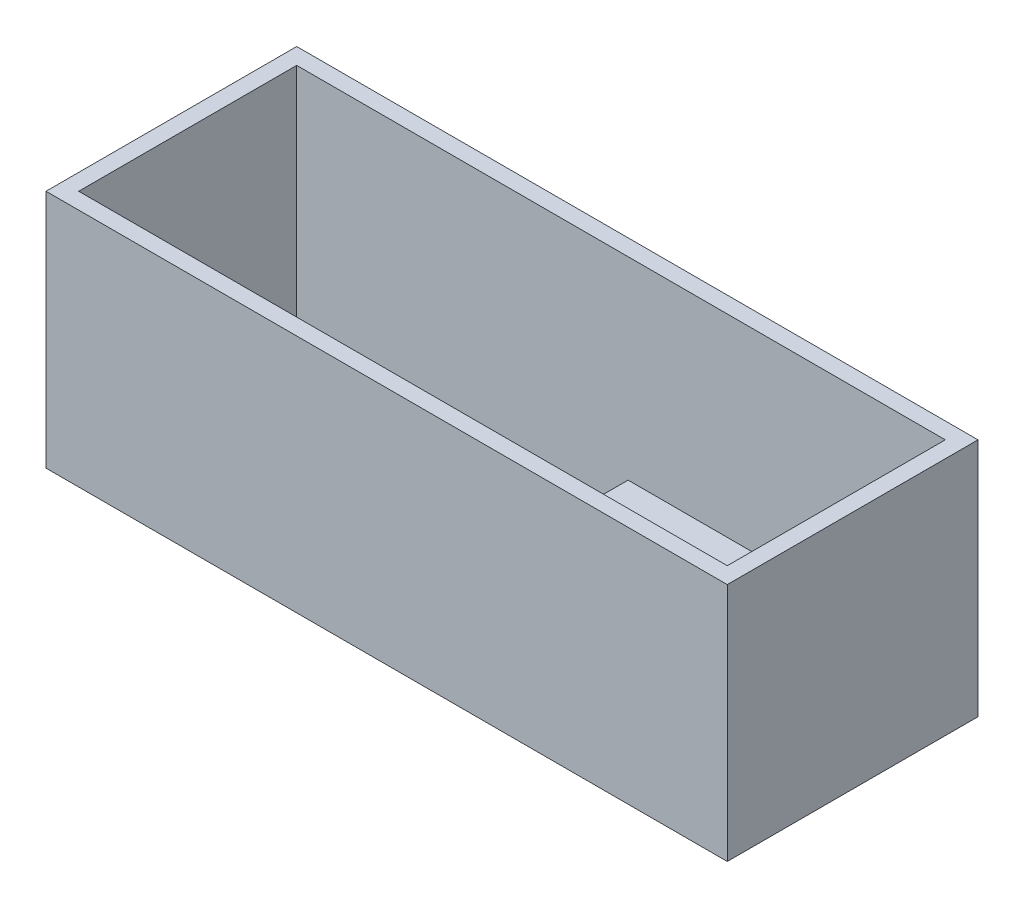
SolidWorks part; units mm, degrees
ref_plane "Front Plane" through (0, 0, 0) normal (0, 0, 1) x (1, 0, 0)
ref_plane "Top Plane" through (0, 0, 0) normal (0, 1, 0) x (1, 0, 0)
ref_plane "Right Plane" through (0, 0, 0) normal (1, 0, 0) x (0, 0, -1)
sketch "Sketch1" plane through (0, 0, 0) normal (0, 1, 0) x (1, 0, 0)
  line L1 (-59.5, -20) -> (59.5, -20)
  line L2 (-59.5, -20) -> (-59.5, 20)
  line L3 (-59.5, 20) -> (59.5, 20)
  line L4 (59.5, -20) -> (59.5, 20)
  line L5 (-59.5, -20) -> (59.5, 20) construction
  line L6 (-59.5, 20) -> (59.5, -20) construction
  point P0 (0, 0)
  dimension "D1" = 119
  dimension "D2" = 40
extrude "Boss-Extrude1" add sketch "Sketch1" along normal blind 4
sketch "Sketch2" plane through (0, 0, 0) normal (0, 1, 0) x (1, 0, 0)
  line L1 (59.5, -20) -> (-59.5, -20)
  line L2 (59.5, -20) -> (59.5, 20)
  line L3 (59.5, 20) -> (-59.5, 20)
  line L4 (-59.5, -20) -> (-59.5, 20)
  line L5 (59.5, -20) -> (-59.5, 20) construction
  line L6 (59.5, 20) -> (-59.5, -20) construction
  line L7 (-62.5, -23) -> (62.5, -23)
  line L8 (-62.5, -23) -> (-62.5, 23)
  line L9 (-62.5, 23) -> (62.5, 23)
  line L10 (62.5, -23) -> (62.5, 23)
  line L11 (-62.5, -23) -> (62.5, 23) construction
  line L12 (-62.5, 23) -> (62.5, -23) construction
  point P0 (0, 0)
  point P7 (0, 0)
  dimension "D1" = 3
  dimension "D2" = 3
extrude "Boss-Extrude2" add sketch "Sketch2" along normal blind 44
sketch "Sketch3" plane through (0, 4, 0) normal (0, 1, 0) x (1, 0, 0)
  line L0 (-59.5, -20) -> (59.5, -20) construction
  line L1 (1.3, -20) -> (59.5, -20)
  line L2 (1.3, -20) -> (1.3, 20)
  line L3 (1.3, 20) -> (59.5, 20)
  line L4 (59.5, -20) -> (59.5, 20)
  dimension "D1" = 58.2
extrude "Boss-Extrude3" add sketch "Sketch3" along normal blind 3
sketch "Sketch4" plane through (0, 7, 0) normal (0, 1, 0) x (1, 0, 0)
  line L0 (1.3, -20) -> (59.5, -20) construction
  line L1 (1.3, 20) -> (29.3, 20)
  line L2 (1.3, 20) -> (1.3, -20)
  line L3 (1.3, -20) -> (29.3, -20)
  line L4 (29.3, 20) -> (29.3, -20)
  dimension "D1" = 28
extrude "Boss-Extrude4" add sketch "Sketch4" along normal blind 1.5
sketch "Sketch5" plane through (0, 0, 0) normal (0, -1, 0) x (1, 0, 0)
  line L0 (62.5, -23) -> (-62.5, -23) construction
  line L1 (62.5, 23) -> (62.5, -23) construction
  circle A0 centre (39.5, 0) radius 4
  dimension "D1" = 8
  dimension "D2" = 23
  dimension "D3" = 23
extrude "Boss-Extrude5" add sketch "Sketch5" along normal blind 12
sketch "Sketch6" plane through (0, 0, 0) normal (0, -1, 0) x (1, 0, 0)
  circle A0 centre (39.5, 0) radius 11.5
  circle A1 centre (39.5, 0) radius 4
  dimension "D1" = 23
extrude "Cut-Extrude1" cut sketch "Sketch6" against normal blind 3
sketch "Sketch7" plane through (0, 3, 0) normal (0, -1, 0) x (1, 0, 0)
  circle A0 centre (39.5, 0) radius 9
  circle A1 centre (39.5, 0) radius 11.5
  dimension "D1" = 18
  dimension "D2" = 23
extrude "Cut-Extrude2" cut sketch "Sketch7" against normal blind 1
